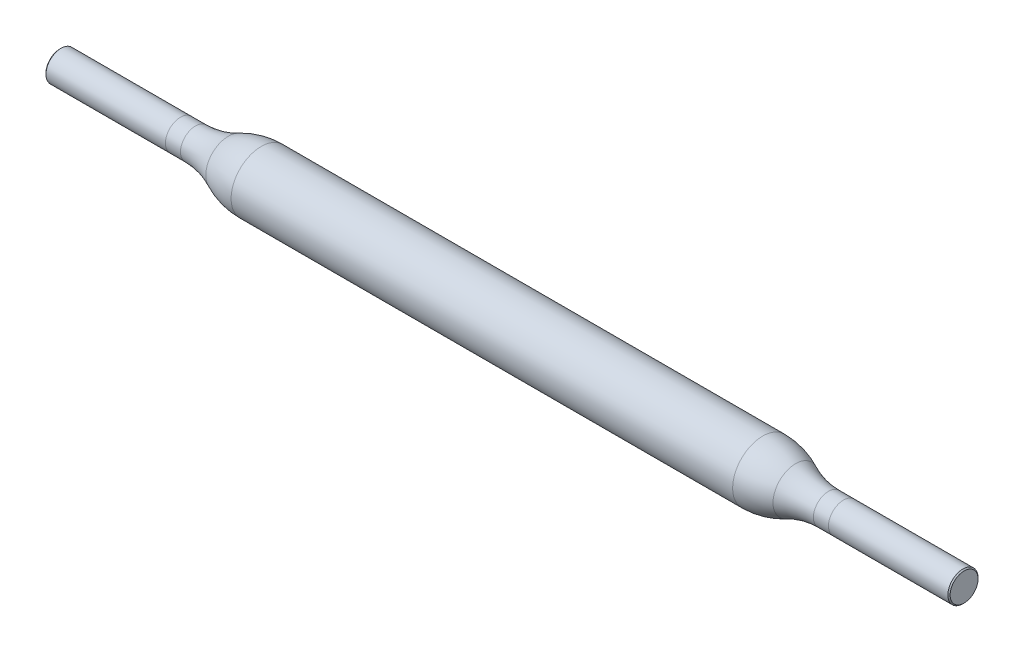
SolidWorks part; units mm, degrees
material "AISI 1045 Acero estirado en frío"
ref_plane "Front Plane" through (0, 0, 0) normal (0, 0, 1) x (1, 0, 0)
ref_plane "Top Plane" through (0, 0, 0) normal (0, 1, 0) x (1, 0, 0)
ref_plane "Right Plane" through (0, 0, 0) normal (1, 0, 0) x (0, 0, -1)
sketch "Sketch1" plane through (0, 0, 0) normal (0, 0, 1) x (1, 0, 0)
  line L0 (-30, 0) -> (30, 0)
  line L1 (-30, 0) -> (-30, 1)
  line L2 (-30, 1) -> (-21, 1)
  line L3 (-16.6411, 2) -> (16.6411, 2)
  line L4 (0, 0) -> (0, 24.5952) construction
  line L5 (30, 0) -> (30, 1)
  line L6 (30, 1) -> (21, 1)
  arc A0 (-21, 1) -> (-18.8206, 1.5) centre (-21, 6) ccw
  arc A1 (21, 1) -> (18.8206, 1.5) centre (21, 6) cw
  arc A2 (18.8206, 1.5) -> (16.6411, 2) centre (16.6411, -3) ccw
  arc A3 (-18.8206, 1.5) -> (-16.6411, 2) centre (-16.6411, -3) cw
  point P4 (0, 0)
  point P15 (0, 2)
  point P17 (18, 2)
  point P20 (-18, 2)
  dimension "D1" = 60
  dimension "D6" = 5
  dimension "D2" = 1
  dimension "D3" = 3
  dimension "D4" = 9
  dimension "D5" = 2
revolve "Revolve1" add sketch "Sketch1" angle 360 about L0
sketch "Sketch2" plane through (0, 0, 0) normal (0, 0, 1) x (1, 0, 0)
  line L0 (0, 0) -> (0, 13.0338) construction
  line L1 (-22, 4.8947) -> (-22, -7.8382)
  line L2 (-30, 1) -> (-30, -1) construction
  line L3 (22, 4.8947) -> (22, -7.8382)
  dimension "D1" = 8
split line "Split Line1"
chamfer "Chamfer1" distance 0.075 angle 45 2 edges at (-30, 0, 1) (30, 0, 1)
ref_plane "Plane1" through (0, 0, 0) normal (-1, 0, 0) x (0, 0, 1)
